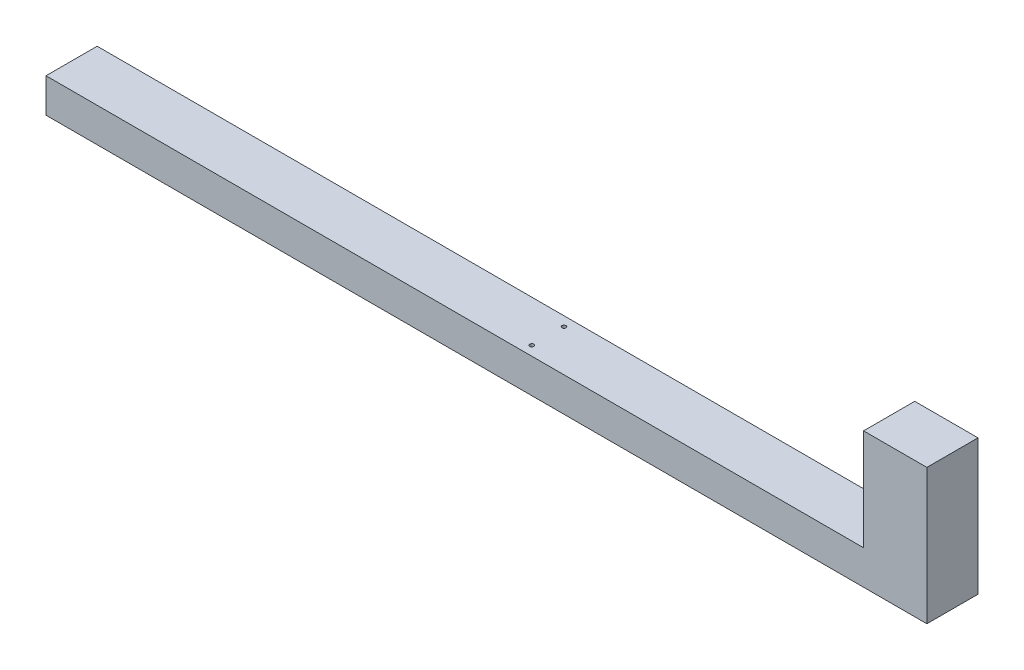
SolidWorks part; units mm, degrees
ref_plane "Front Plane" through (0, 0, 0) normal (0, 0, 1) x (1, 0, 0)
ref_plane "Top Plane" through (0, 0, 0) normal (0, 1, 0) x (1, 0, 0)
ref_plane "Right Plane" through (0, 0, 0) normal (1, 0, 0) x (0, 0, -1)
sketch "Sketch1" plane through (0, 0, 0) normal (0, 1, 0) x (1, 0, 0)
  line L1 (559.5, -35) -> (-559.5, -35)
  line L2 (559.5, -35) -> (559.5, 35)
  line L3 (559.5, 35) -> (-559.5, 35)
  line L4 (-559.5, -35) -> (-559.5, 35)
  line L5 (559.5, -35) -> (-559.5, 35) construction
  line L6 (559.5, 35) -> (-559.5, -35) construction
  point P0 (0, 0)
  dimension "D1" = 1119
  dimension "D2" = 70
extrude "Boss-Extrude1" add sketch "Sketch1" along normal blind 46.8
sketch "Sketch2" plane through (0, 0, 0) normal (0, -1, 0) x (1, 0, 0)
  line L1 (559.5, 35) -> (646.1, 35)
  line L2 (559.5, 35) -> (559.5, -35)
  line L3 (559.5, -35) -> (646.1, -35)
  line L4 (646.1, 35) -> (646.1, -35)
  dimension "D1" = 86.6
extrude "Boss-Extrude2" add sketch "Sketch2" against normal blind 185.4
sketch "Sketch4" plane through (0, 46.8, 0) normal (0, 1, 0) x (1, 0, 0)
  line L0 (92.4786, -35) -> (92.4786, 35) construction
  line L2 (-559.5, -35) -> (559.5, -35) construction
  line L3 (559.5, 35) -> (-559.5, 35) construction
  circle A0 centre (92.4786, 22) radius 2.75
  circle A1 centre (92.4786, -22) radius 2.75
  point P13 (92.4786, 0)
  dimension "D1" = 5.5
  dimension "D2" = 5.5
  dimension "D3" = 44
  dimension "D4" = 22
extrude "Cut-Extrude1" cut sketch "Sketch4" against normal blind 10
